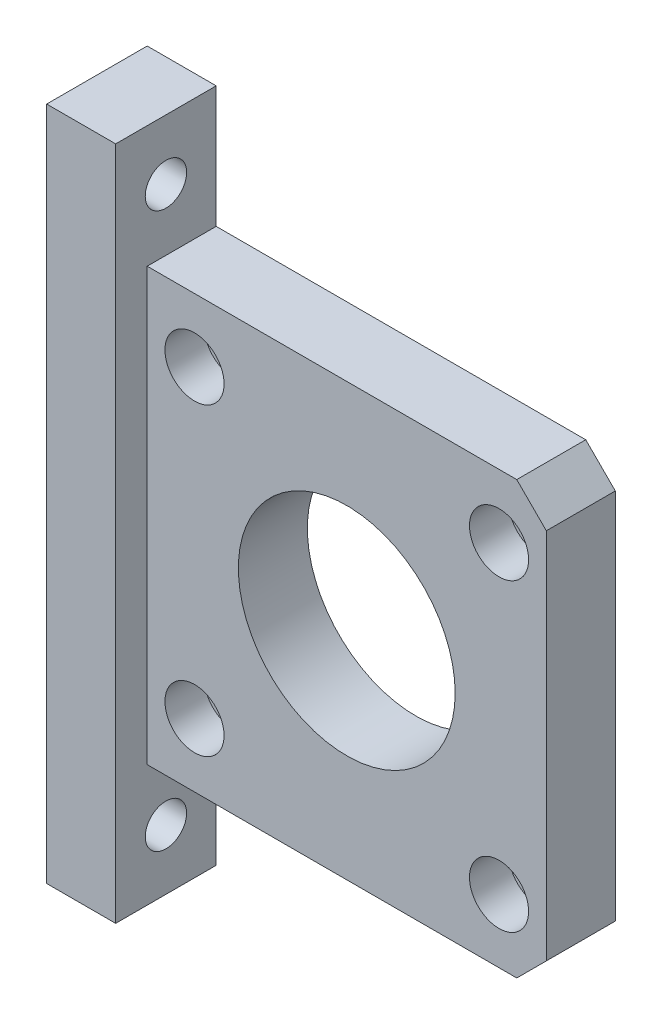
SolidWorks part; units mm, degrees
ref_plane "Alzado" through (0, 0, 0) normal (0, 0, 1) x (1, 0, 0)
ref_plane "Planta" through (0, 0, 0) normal (0, 1, 0) x (1, 0, 0)
ref_plane "Vista lateral" through (0, 0, 0) normal (1, 0, 0) x (0, 0, -1)
sketch "Croquis1" plane through (0, 0, 0) normal (0, 0, 1) x (1, 0, 0)
  line L0 (17.25, -21.9) -> (20.25, -18.9)
  line L1 (-20.25, -21.9) -> (17.25, -21.9)
  line L2 (-20.25, -21.9) -> (-20.25, 21.9)
  line L3 (-20.25, 21.9) -> (17.25, 21.9)
  line L4 (20.25, -18.9) -> (20.25, 18.9)
  line L5 (-20.25, -21.9) -> (20.25, 21.9) construction
  line L6 (-20.25, 21.9) -> (20.25, -21.9) construction
  line L7 (-40, -40) -> (40, -40) construction
  line L8 (-40, -40) -> (-40, 40) construction
  line L9 (-40, 40) -> (40, 40) construction
  line L10 (40, -40) -> (40, 40) construction
  line L11 (-40, -40) -> (40, 40) construction
  line L12 (-40, 40) -> (40, -40) construction
  line L13 (17.25, 21.9) -> (20.25, 18.9)
  circle A0 centre (0, 0) radius 11
  circle A2 centre (15.4503, 15.4503) radius 1.75
  circle A3 centre (15.4503, -15.4503) radius 1.75
  circle A4 centre (-15.4503, -15.4503) radius 1.75
  circle A5 centre (-15.4503, 15.4503) radius 1.75
  point P22 (0, 0)
  dimension "D1" = 22
  dimension "D5" = 80
  dimension "D6" = 3.5
  dimension "D2" = 40.5
  dimension "D3" = 43.8
  dimension "D4" = 80
  dimension "D9" = 21.85
  dimension "D7" = 4
extrude "Saliente-Extruir1" add sketch "Croquis1" along normal blind 7
sketch "Croquis2" plane through (0, 0, 7) normal (0, 0, 1) x (1, 0, 0)
  circle A0 centre (15.4503, 15.4503) radius 3
  circle A1 centre (15.4503, -15.4503) radius 3
  circle A2 centre (-15.4503, -15.4503) radius 3
  circle A3 centre (-15.4503, 15.4503) radius 3
  point P12 (0, 0)
  dimension "D1" = 6
  dimension "D2" = 4
extrude "Cortar-Extruir1" cut sketch "Croquis2" against normal blind 4
sketch "Croquis3" plane through (0, 0, 0) normal (0, 0, -1) x (-1, 0, 0)
  line L0 (20.25, 21.9) -> (20.25, -21.9) construction
  line L1 (20.25, 34.25) -> (27.25, 34.25)
  line L2 (20.25, 34.25) -> (20.25, -34.25)
  line L3 (20.25, -34.25) -> (27.25, -34.25)
  line L4 (27.25, 34.25) -> (27.25, -34.25)
  point P4 (20.25, 0)
  point P7 (20.25, 0)
  dimension "D1" = 7
  dimension "D2" = 68.5
extrude "Saliente-Extruir2" add sketch "Croquis3" against normal blind 10.2
sketch "Croquis4" plane through (-27.25, 0, 0) normal (-1, 0, 0) x (0, 0, 1)
  line L0 (10.2, 0) -> (0, 0) construction
  line L1 (10.2, -34.25) -> (10.2, 34.25) construction
  line L2 (0, -34.25) -> (0, 34.25) construction
  circle A0 centre (5.1, 28.15) radius 2.1
  circle A1 centre (5.1, -28.15) radius 2.1
  dimension "D2" = 4.2
  dimension "D1" = 28.15
extrude "Cortar-Extruir2" cut sketch "Croquis4" against normal up to vertex (7 mm away)
